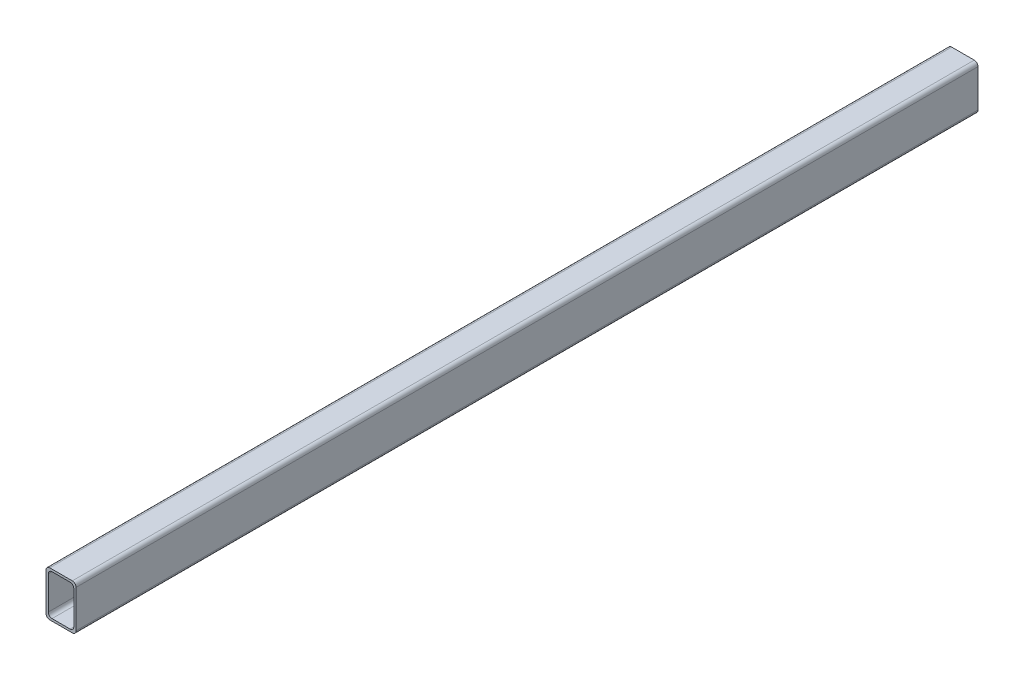
SolidWorks part; units mm, degrees
ref_plane "Alzado" through (0, 0, 0) normal (0, 0, 1) x (1, 0, 0)
ref_plane "Planta" through (0, 0, 0) normal (0, 1, 0) x (1, 0, 0)
ref_plane "Vista lateral" through (0, 0, 0) normal (1, 0, 0) x (0, 0, -1)
sketch "Croquis1" plane through (0, 0, 0) normal (0, 0, 1) x (1, 0, 0)
  line L1 (-15, -30) -> (15, -30)
  line L2 (-20, -25) -> (-20, 25)
  line L3 (-15, 30) -> (15, 30)
  line L4 (20, -25) -> (20, 25)
  line L5 (-20, -30) -> (20, 30) construction
  line L6 (-20, 30) -> (20, -30) construction
  line L7 (-12, -27) -> (12, -27)
  line L8 (-17, -22) -> (-17, 22)
  line L9 (-12, 27) -> (12, 27)
  line L10 (17, -22) -> (17, 22)
  line L11 (-17, -27) -> (17, 27) construction
  line L12 (-17, 27) -> (17, -27) construction
  arc A0 (-15, -30) -> (-20, -25) centre (-15, -25) cw
  arc A1 (15, -30) -> (20, -25) centre (15, -25) ccw
  arc A2 (15, 30) -> (20, 25) centre (15, 25) cw
  arc A3 (-20, 25) -> (-15, 30) centre (-15, 25) cw
  arc A4 (12, 27) -> (17, 22) centre (12, 22) cw
  arc A5 (12, -27) -> (17, -22) centre (12, -22) ccw
  arc A6 (-12, -27) -> (-17, -22) centre (-12, -22) cw
  arc A7 (-17, 22) -> (-12, 27) centre (-12, 22) cw
  point P0 (0, 0)
  point P18 (0, 0)
  dimension "D3" = 5
  dimension "D6" = 5
  dimension "D1" = 40
  dimension "D2" = 60
  dimension "D4" = 34
  dimension "D5" = 54
extrude "Saliente-Extruir1" add sketch "Croquis1" along normal blind 1200
